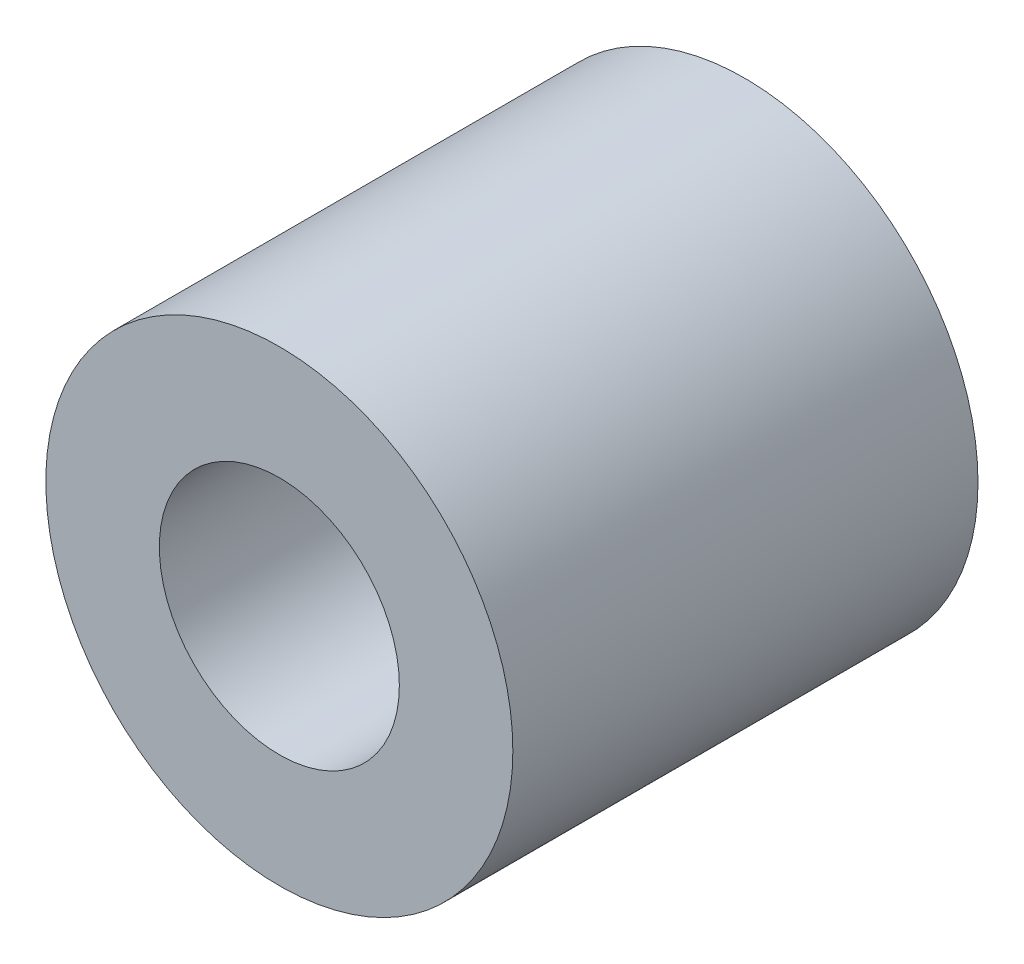
SolidWorks part; units mm, degrees
ref_plane "Front Plane" through (0, 0, 0) normal (0, 0, 1) x (1, 0, 0)
ref_plane "Top Plane" through (0, 0, 0) normal (0, 1, 0) x (1, 0, 0)
ref_plane "Right Plane" through (0, 0, 0) normal (1, 0, 0) x (0, 0, -1)
sketch "Sketch1" plane through (0, 0, 0) normal (0, 0, 1) x (1, 0, 0)
  circle A0 centre (0, 0) radius 3.1877
  circle A1 centre (0, 0) radius 1.6383
  dimension "D1" = 6.3754
  dimension "ID" = 3.2766
extrude "Extrude1" add sketch "Sketch1" along normal mid plane 6.35
sketch "Sketch2" plane through (0, 0, 0) normal (1, 0, 0) x (0, 0, -1)
  line L0 (-3.175, -1.6383) -> (3.175, -1.6383) construction
  line L3 (3.175, 1.6383) -> (-3.175, 1.6383) construction
  line L5 (-3.175, -1.6383) -> (3.175, -1.6383)
  line L6 (3.175, 1.6383) -> (-3.175, 1.6383)
sketch "Sketch4" plane through (0, 0, 3.175) normal (0, 0, 1) x (1, 0, 0)
  line L0 (0, 0) -> (-1.1585, 1.1585)
  line L1 (0, -6.985) -> (0, 6.985) construction
  circle A0 centre (0, 0) radius 1.6383 construction
  dimension "D1" = 45
